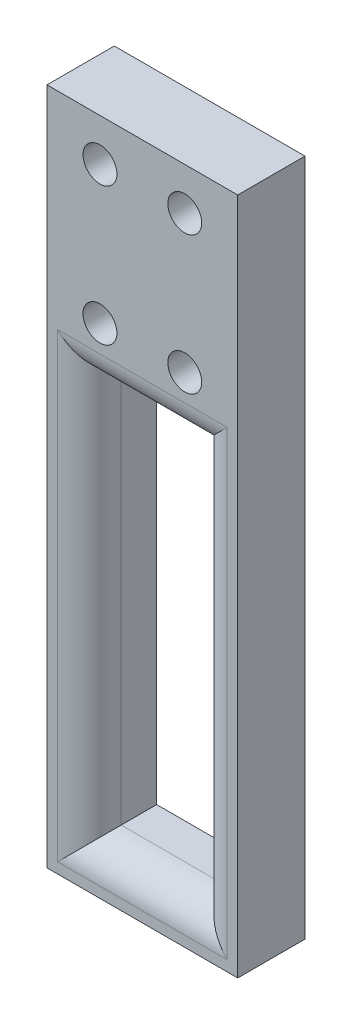
SolidWorks part; units mm, degrees
ref_plane "Front" through (0, 0, 0) normal (0, 0, 1) x (1, 0, 0)
ref_plane "Top" through (0, 0, 0) normal (0, 1, 0) x (1, 0, 0)
ref_plane "Right" through (0, 0, 0) normal (1, 0, 0) x (0, 0, -1)
sketch "Sketch1" plane through (0, 0, 0) normal (0, 0, 1) x (1, 0, 0)
  line L1 (-9, -32) -> (9, -32)
  line L2 (-9, -32) -> (-9, 32)
  line L3 (-9, 32) -> (9, 32)
  line L4 (9, -32) -> (9, 32)
  line L5 (-9, -32) -> (9, 32) construction
  line L6 (-9, 32) -> (9, -32) construction
  point P0 (0, 0)
  dimension "D1" = 18
  dimension "D2" = 64
extrude "Boss-Extrude1" add sketch "Sketch1" along normal blind 6.35
sketch "Sketch2" plane through (0, 0, 6.35) normal (0, 0, 1) x (1, 0, 0)
  line L0 (0, 0) -> (0, 21.5) construction
  line L1 (-4, 15) -> (4, 15) construction
  line L2 (-4, 15) -> (-4, 28) construction
  line L3 (-4, 28) -> (4, 28) construction
  line L4 (4, 15) -> (4, 28) construction
  line L5 (-4, 15) -> (4, 28) construction
  line L6 (-4, 28) -> (4, 15) construction
  line L7 (9, 32) -> (-9, 32) construction
  point P0 (0, 21.5)
  dimension "D1" = 8
  dimension "D2" = 13
  dimension "D3" = 4
hole_wizard "M3 Clearance Hole1" positions "3DSketch1" profile "Sketch3" hole size "M3" standard "ANSI Metric"
sketch3d "3DSketch1"
  point P0 (-4, 15, 6.35)
  point P3 (-4, 28, 6.35)
  point P6 (4, 28, 6.35)
  point P9 (4, 15, 6.35)
sketch "Sketch3" plane through (-4, 15, 6.35) normal (1, 0, 0) x (0, -1, 0)
  line L0 (0, 0) -> (0, 8.4614)
  line L1 (0, 8.4614) -> (1.6, 7.5)
  line L2 (1.6, 7.5) -> (1.6, 0)
  line L5 (1.6, 0) -> (0, 0)
  line L10 (0, 8.4614) -> (-1.6, 7.5) construction
  line L11 (0, -6.35) -> (0, 107.95) construction
  dimension "Hole Dia." = 3.2
  dimension "Hole Depth" = 7.5
  dimension "Drill Angle" = 118
sketch "Sketch4" plane through (0, 0, 6.35) normal (0, 0, 1) x (1, 0, 0)
  line L0 (-9, -32) -> (9, -32) construction
  line L1 (-5, -28) -> (5, -28)
  line L2 (-5, -28) -> (-5, 9.5)
  line L3 (-5, 9.5) -> (5, 9.5)
  line L4 (5, -28) -> (5, 9.5)
  line L5 (-5, -28) -> (5, 9.5) construction
  line L6 (-5, 9.5) -> (5, -28) construction
  line L7 (9, -32) -> (9, 32) construction
  line L8 (0, -9.25) -> (0, 0) construction
  circle A0 centre (4, 15) radius 1.6 construction
  point P0 (0, -9.25)
  dimension "D1" = 4
  dimension "D2" = 4
  dimension "D3" = 5.5
extrude "Cut-Extrude1" cut sketch "Sketch4" against normal through all
fillet "Fillet1" radius 3 4 edges at (5, -9.25, 6.35) (0, -28, 6.35) (-5, -9.25, 6.35) (0, 9.5, 6.35)
